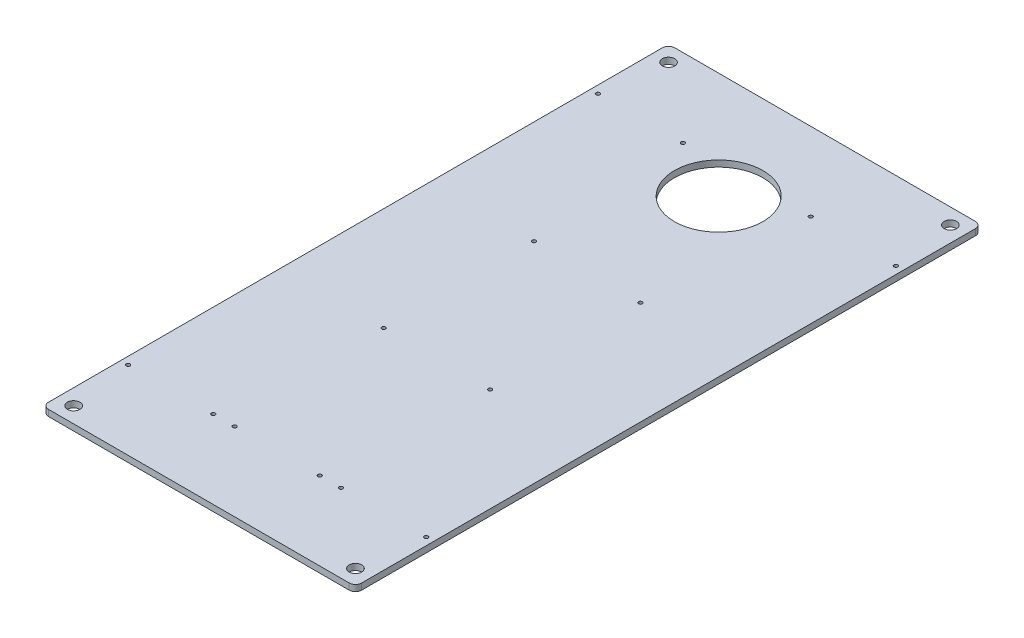
SolidWorks part; units mm, degrees
material "AISI 1045 Steel, cold drawn"
ref_plane "Front Plane" through (0, 0, 0) normal (0, 0, 1) x (1, 0, 0)
ref_plane "Top Plane" through (0, 0, 0) normal (0, 1, 0) x (1, 0, 0)
ref_plane "Right Plane" through (0, 0, 0) normal (1, 0, 0) x (0, 0, -1)
sketch "Sketch1" plane through (0, 0, 0) normal (0, 1, 0) x (1, 0, 0)
  line L1 (-250, -500) -> (250, -500)
  line L2 (-250, -500) -> (-250, 500)
  line L3 (-250, 500) -> (250, 500)
  line L4 (250, -500) -> (250, 500)
  line L5 (-250, -500) -> (250, 500) construction
  line L6 (-250, 500) -> (250, -500) construction
  point P0 (0, 0)
  dimension "D1" = 500
  dimension "D2" = 1000
extrude "Boss-Extrude1" add sketch "Sketch1" along normal blind 10
sketch "Sketch2" plane through (0, 10, 0) normal (0, 1, 0) x (1, 0, 0)
  line L0 (250, 500) -> (-250, 500) construction
  line L1 (-250, 500) -> (-250, -500) construction
  line L2 (0, 0) -> (0, 500) construction
  line L3 (0, 0) -> (250, 0) construction
  line L4 (250, -500) -> (250, 500) construction
  circle A0 centre (-225, 475) radius 10
  circle A1 centre (225, 475) radius 10
  circle A2 centre (-225, -475) radius 10
  circle A3 centre (225, -475) radius 10
  dimension "D1" = 20
  dimension "D2" = 25
  dimension "D3" = 25
extrude "lo bat xuong dat" cut sketch "Sketch2" against normal up to next
fillet "Fillet1" radius 10 4 edges at (-250, 5, 500) (-250, 5, -500) (250, 5, -500) (250, 5, 500)
sketch "Sketch3" plane through (0, 10, 0) normal (0, 1, 0) x (1, 0, 0)
  line L0 (0, 0) -> (0, 330) construction
  circle A0 centre (0, 330) radius 70.65
  dimension "D1" = 141.3
  dimension "D2" = 330
extrude "Cut-Extrude2" cut sketch "Sketch3" against normal up to next
sketch "Sketch4" plane through (0, 10, 0) normal (0, 1, 0) x (1, 0, 0)
  line L1 (-85, -120) -> (85, -120) construction
  line L2 (-85, -120) -> (-85, 120) construction
  line L3 (-85, 120) -> (85, 120) construction
  line L4 (85, -120) -> (85, 120) construction
  line L5 (-85, -120) -> (85, 120) construction
  line L6 (-85, 120) -> (85, -120) construction
  circle A0 centre (-85, 120) radius 3
  circle A1 centre (85, 120) radius 3
  circle A2 centre (85, -120) radius 3
  circle A3 centre (-85, -120) radius 3
  point P0 (0, 0)
  dimension "D3" = 6
  dimension "D1" = 170
  dimension "D2" = 240
extrude "bat chan de khop noi" cut sketch "Sketch4" against normal up to next
sketch "Sketch5" plane through (0, 10, 0) normal (0, 1, 0) x (1, 0, 0)
  line L0 (-49.9571, 379.9571) -> (49.9571, 280.0429)
  line L1 (0, 330) -> (0, 259.35) construction
  line L2 (49.9571, 379.9571) -> (-49.9571, 280.0429)
  circle A0 centre (0, 330) radius 70.65 construction
  point P9 (0, 330)
  dimension "D1" = 45
sketch "Sketch6" plane through (0, 10, 0) normal (0, 1, 0) x (1, 0, 0)
  line L0 (-240, -500) -> (240, -500) construction
  line L1 (250, -490) -> (250, 490) construction
  line L2 (238, -375) -> (170, -375) construction
  line L3 (170, -375) -> (170, -349.8809) construction
  line L4 (0, -500) -> (0, -181.1688) construction
  line L5 (0, 0) -> (250, 0) construction
  circle A0 centre (238, -375) radius 3
  circle A2 centre (102, -375) radius 3
  circle A5 centre (-102, -375) radius 3
  circle A7 centre (-238, -375) radius 3
  circle A8 centre (-238, 375) radius 3
  circle A10 centre (-102, 375) radius 3
  circle A13 centre (102, 375) radius 3
  circle A15 centre (238, 375) radius 3
  circle A16 centre (68, -375) radius 3
  circle A17 centre (-68, -375) radius 3
  dimension "D1" = 6
  dimension "D2" = 125
  dimension "D3" = 12
  dimension "D4" = 68
  dimension "D6" = 68
  dimension "D5" = 68
extrude "Cut-Extrude3" cut sketch "Sketch6" against normal up to next
